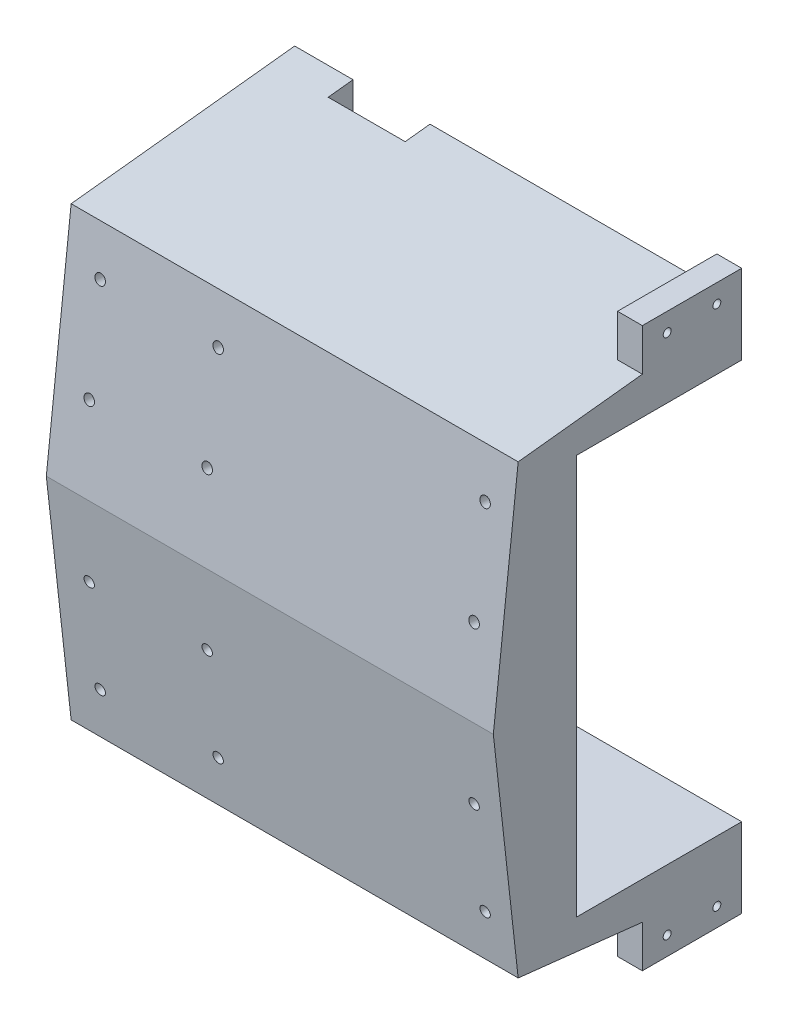
SolidWorks part; units mm, degrees
material "PETG"
ref_plane "Plan de face" through (0, 0, 0) normal (0, 0, 1) x (1, 0, 0)
ref_plane "Plan de dessus" through (0, 0, 0) normal (0, 1, 0) x (1, 0, 0)
ref_plane "Plan de droite" through (0, 0, 0) normal (1, 0, 0) x (0, 0, -1)
sketch "Sketch5" plane through (0, 0, 0) normal (1, 0, 0) x (0, 0, -1)
  line L0 (0, 0) -> (10, 90)
  line L1 (10, 90) -> (100, 100)
  line L2 (100, 100) -> (100, -100)
  line L3 (0, 0) -> (10, -90)
  line L4 (10, -90) -> (100, -100)
  point P8 (100, 0)
  dimension "D1" = 200
  dimension "D2" = 100
  dimension "D3" = 10
  dimension "D5" = 90
extrude "Boss-Extrude1" add sketch "Sketch5" against normal blind 10
sketch "Sketch6" plane through (0, 0, 0) normal (1, 0, 0) x (0, 0, -1)
  line L2 (0, 0) -> (10, -90)
  line L3 (10, -90) -> (100, -100)
  line L4 (100, -100) -> (100, -90)
  line L5 (100, -100) -> (100, 100) construction
  line L6 (100, -90) -> (19, -81)
  line L7 (19, -81) -> (10, 0)
  line L11 (55, 0) -> (-55, 0) construction
  line L12 (19, 81) -> (10, 0)
  line L13 (100, 90) -> (19, 81)
  line L14 (100, 100) -> (100, 90)
  line L15 (10, 90) -> (100, 100)
  line L16 (0, 0) -> (10, 90)
  dimension "D2" = 10
  dimension "D4" = 10
extrude "Boss-Extrude2" add sketch "Sketch6" along normal blind 170
sketch "Sketch7" plane through (170, 0, 0) normal (1, 0, 0) x (0, 0, -1)
  line L0 (19, 81) -> (10, 0)
  line L1 (10, 0) -> (19, -81)
  line L2 (19, -81) -> (33.5, -82.6111)
  line L3 (100, -90) -> (19, -81) construction
  line L4 (33.5, -82.6111) -> (33.5, 82.6111)
  line L5 (19, 81) -> (100, 90) construction
  line L6 (33.5, 82.6111) -> (19, 81)
  dimension "D1" = 23.5
extrude "Boss-Extrude3" add sketch "Sketch7" against normal up to next
sketch "Sketch8" plane through (0, 0, -100) normal (0, 0, -1) x (-1, 0, 0)
  line L0 (0, 82.6111) -> (0, -82.6111) construction
  line L1 (-170, 90) -> (0, 90)
  line L2 (-170, 90) -> (-170, 80.5)
  line L3 (-170, 80.5) -> (0, 80.5)
  line L4 (0, 90) -> (0, 80.5)
  line L5 (55, 0) -> (-55, 0) construction
  line L6 (0, -90) -> (0, -80.5)
  line L7 (-170, -80.5) -> (0, -80.5)
  line L8 (-170, -90) -> (-170, -80.5)
  line L9 (-170, -90) -> (0, -90)
  dimension "D1" = 9.5
extrude "Boss-Extrude4" add sketch "Sketch8" against normal up to next
sketch "Sketch9" plane through (0, 0, -100) normal (0, 0, -1) x (-1, 0, 0)
  line L0 (0, 80.5) -> (0, -80.5) construction
  line L1 (-13.5, -100) -> (-44.5, -100)
  line L2 (-13.5, -100) -> (-13.5, -80.5)
  line L3 (-13.5, -80.5) -> (-44.5, -80.5)
  line L4 (-44.5, -100) -> (-44.5, -80.5)
  line L5 (-13.5, -100) -> (-44.5, -80.5) construction
  line L6 (-13.5, -80.5) -> (-44.5, -100) construction
  line L7 (10, -100) -> (-170, -100) construction
  line L8 (-170, -80.5) -> (0, -80.5) construction
  line L9 (55, 0) -> (-55, 0) construction
  line L10 (-13.5, 100) -> (-13.5, 80.5)
  line L11 (-13.5, 100) -> (-44.5, 100)
  line L12 (-44.5, 100) -> (-44.5, 80.5)
  line L13 (-13.5, 80.5) -> (-44.5, 80.5)
  point P0 (-29, -90.25)
  dimension "D1" = 29
  dimension "D2" = 31
extrude "Cut-Extrude1" cut sketch "Sketch9" against normal blind 10
sketch "Sketch10" plane through (0, 0, -100) normal (0, 0, -1) x (-1, 0, 0)
  line L1 (-13.5, -100) -> (-13.5, -80.5) construction
  line L3 (55, 0) -> (-55, 0) construction
  line L8 (0, -80.5) -> (-13.5, -80.5) construction
  circle A0 centre (-22, -90.25) radius 2.1
  circle A1 centre (-22, 90.25) radius 2.1
  circle A2 centre (-36, -90.25) radius 2.1
  circle A3 centre (-36, 90.25) radius 2.1
  dimension "D1" = 4.2
  dimension "D2" = 9.75
  dimension "D3" = 8.5
  dimension "D4" = 14
extrude "Cut-Extrude2" cut sketch "Sketch10" against normal offset from surface (20 mm away) 10 up to face at (29, -89.6944, -90) offset beyond the face yes
hole_wizard "Ø4.0mm Dowel Hole1" positions "Sketch11" profile "Sketch12" hole size "Ø4.0" standard "ANSI Metric"
sketch "Sketch11" plane through (0, 0, -100) normal (0, 0, -1) x (-1, 0, 0)
  point P0 (-157.5, 90.25)
  point P3 (-137.5, 90.25)
  point P6 (-117.5, 90.25)
  point P9 (-97.5, 90.25)
  point P12 (-77.5, 90.25)
  point P15 (-57.5, 90.25)
  point P18 (-157.5, -90.25)
  point P21 (-137.5, -90.25)
  point P24 (-117.5, -90.25)
  point P27 (-97.5, -90.25)
  point P30 (-77.5, -90.25)
  point P33 (-57.5, -90.25)
sketch "Sketch12" plane through (157.5, 90.25, -100) normal (1, 0, 0) x (0, 1, 0)
  line L0 (0, 0) -> (0, 11.2618)
  line L1 (0, 11.2618) -> (2.1, 10)
  line L2 (2.1, 10) -> (2.1, 0)
  line L5 (2.1, 0) -> (0, 0)
  line L10 (0, 11.2618) -> (-2.1, 10) construction
  line L11 (0, -6.35) -> (0, 107.95) construction
  dimension "Hole Dia." = 4.2
  dimension "Hole Depth" = 10
  dimension "Drill Angle" = 118
sketch "Sketch13" plane through (0, 0, 0) normal (0, -0.1104, 0.9939) x (1, 0, 0)
  circle A0 centre (51.25, -31.9444) radius 1.6 construction
  circle A1 centre (3.75, -31.9444) radius 1.6 construction
  circle A2 centre (51.25, -71.9444) radius 1.6 construction
  circle A3 centre (3.75, -71.9444) radius 1.6 construction
  circle A4 centre (51.25, -31.9444) radius 1.6 construction
  circle A5 centre (3.75, -31.9444) radius 1.6 construction
  circle A6 centre (51.25, -71.9444) radius 1.6 construction
  circle A7 centre (3.75, -71.9444) radius 1.6 construction
  circle A8 centre (158.75, -31.8889) radius 1.6 construction
  circle A9 centre (158.75, -71.8889) radius 1.6 construction
  circle A10 centre (158.75, -31.8889) radius 1.6 construction
  circle A11 centre (158.75, -71.8889) radius 1.6 construction
  circle A12 centre (3.75, -31.9444) radius 2.1
  circle A13 centre (51.25, -31.9444) radius 2.1
  circle A14 centre (3.75, -71.9444) radius 2.1
  circle A15 centre (51.25, -71.9444) radius 2.1
  circle A16 centre (158.75, -31.8889) radius 2.1
  circle A17 centre (158.75, -71.8889) radius 2.1
  dimension "D1" = 4.2
extrude "Cut-Extrude3" cut sketch "Sketch13" against normal blind 10
mirror "Mirror1" about plane through (0, 0, 0) normal (0, 1, 0) of "Cut-Extrude3"
sketch "Sketch14" plane through (170, 0, 0) normal (1, 0, 0) x (0, 0, -1)
  line L0 (60, 95.5556) -> (100, 100)
  line L1 (60, 95.5556) -> (60, 112.5)
  line L2 (100, 100) -> (100, 112.5)
  line L3 (60, 112.5) -> (100, 112.5)
  line L4 (100, 100) -> (10, 90) construction
  line L5 (55, 0) -> (-55, 0) construction
  line L6 (100, -100) -> (100, -112.5)
  line L7 (60, -95.5556) -> (100, -100)
  line L8 (60, -95.5556) -> (60, -112.5)
  line L9 (60, -112.5) -> (100, -112.5)
  line L10 (100, 80.5) -> (100, 100) construction
  dimension "D1" = 40
  dimension "D2" = 12.5
extrude "Boss-Extrude5" add sketch "Sketch14" against normal blind 10
sketch "Sketch15" plane through (170, 0, 0) normal (1, 0, 0) x (0, 0, -1)
  line L0 (60, -95.5556) -> (60, -112.5) construction
  line L2 (60, -105) -> (100, -105) construction
  line L3 (55, 0) -> (-55, 0) construction
  line L4 (100, -112.5) -> (100, -80.5) construction
  line L5 (60, -112.5) -> (100, -112.5) construction
  circle A0 centre (70, -105) radius 1.6
  circle A1 centre (90, -105) radius 1.6
  circle A2 centre (90, 105) radius 1.6
  circle A3 centre (70, 105) radius 1.6
  point P4 (60, -105)
  point P8 (100, -105)
  dimension "D1" = 3.2
  dimension "D2" = 10
  dimension "D3" = 10
  dimension "D4" = 7.5
extrude "Cut-Extrude4" cut sketch "Sketch15" against normal up to next
